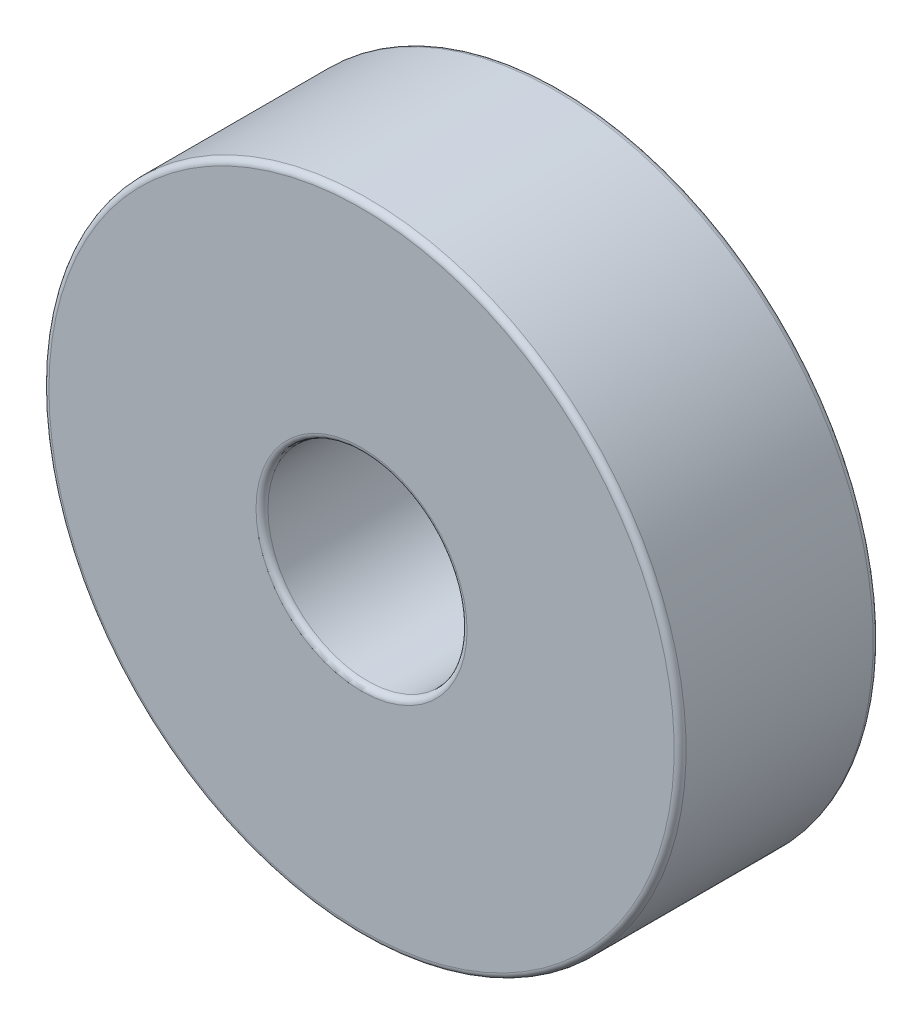
SolidWorks part; units mm, degrees
material "Chrome Stainless Steel"
ref_plane "Front Plane" through (0, 0, 0) normal (0, 0, 1) x (1, 0, 0)
ref_plane "Top Plane" through (0, 0, 0) normal (0, 1, 0) x (1, 0, 0)
ref_plane "Right Plane" through (0, 0, 0) normal (1, 0, 0) x (0, 0, -1)
sketch "Sketch1" plane through (0, 0, 0) normal (1, 0, 0) x (0, 0, -1)
  line L0 (0, 0) -> (-17.0468, 0) construction
  line L1 (5, 2.65) -> (5, 7.85)
  line L4 (4.85, 8) -> (0.15, 8)
  line L5 (0, 7.85) -> (0, 2.65)
  line L6 (0.15, 2.5) -> (4.85, 2.5)
  arc A0 (0.15, 2.5) -> (0, 2.65) centre (0.15, 2.65) cw
  arc A1 (4.85, 2.5) -> (5, 2.65) centre (4.85, 2.65) ccw
  arc A2 (0.15, 8) -> (0, 7.85) centre (0.15, 7.85) ccw
  arc A4 (5, 7.85) -> (4.85, 8) centre (4.85, 7.85) ccw
  dimension "D6" = 0.15
  dimension "D1" = 2.5
  dimension "D2" = 8
  dimension "D3" = 5
revolve "Revolve1" add sketch "Sketch1" angle 360 about L0
